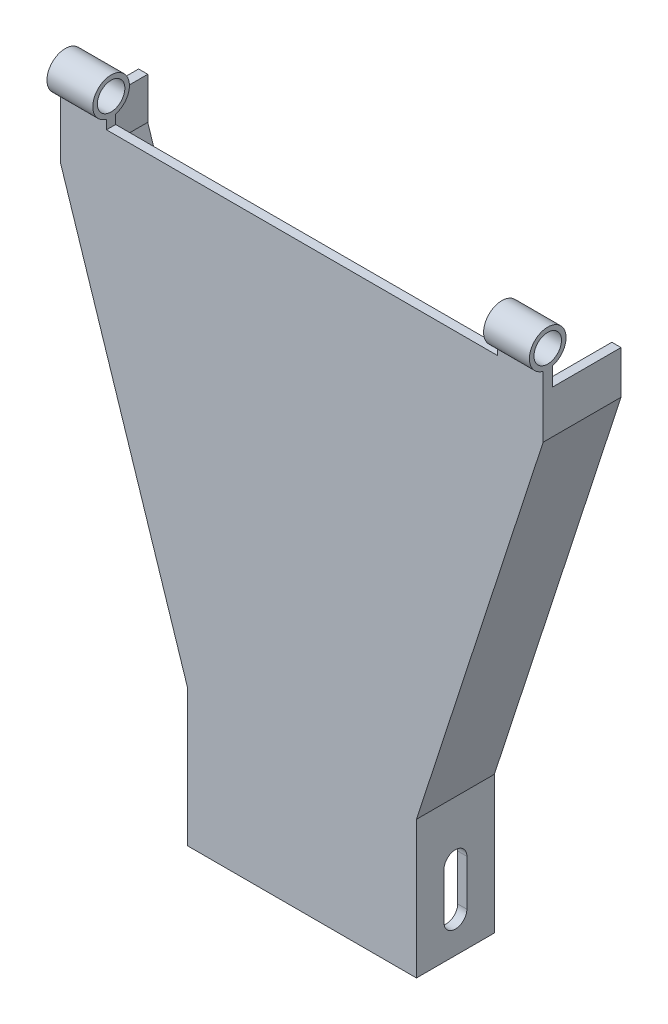
SolidWorks part; units mm, degrees
ref_plane "Front Plane" through (0, 0, 0) normal (0, 0, 1) x (1, 0, 0)
ref_plane "Top Plane" through (0, 0, 0) normal (0, 1, 0) x (1, 0, 0)
ref_plane "Right Plane" through (0, 0, 0) normal (1, 0, 0) x (0, 0, -1)
sketch "Sketch1" plane through (0, 0, 0) normal (0, 0, 1) x (1, 0, 0)
  line L1 (-52.65, -30.4) -> (-25, -115.5)
  line L2 (-25, -115.5) -> (-25, -145.5)
  line L3 (-42.65, -17) -> (-42.65, -19)
  line L4 (52.65, -30.4) -> (25, -115.5)
  line L5 (-42.65, -19) -> (42.65, -19)
  line L6 (42.65, -19) -> (42.65, -17)
  line L7 (25, -115.5) -> (25, -145.5)
  line L9 (52.65, -17) -> (52.65, -30.4)
  line L11 (25, -145.5) -> (-25, -145.5)
  line L13 (-52.65, -30.4) -> (-52.65, -17)
  line L14 (16, -30.4) -> (-16, -30.4) construction
  line L16 (42.15, -14) -> (53.15, -14) construction
  line L20 (18.1, -17) -> (42.15, -17) construction
  line L21 (-115.8448, -115.5) -> (115.8448, -115.5) construction
  line L22 (42.65, -17) -> (52.65, -17)
  line L23 (-52.65, -17) -> (-42.65, -17)
  line L24 (-42.15, -17) -> (-18.1, -17) construction
  line L25 (-42.15, -14) -> (-53.15, -14) construction
  circle A1 centre (0, 0) radius 115.5 construction
  point P16 (47.65, -14)
  point P22 (0, -115.5)
  point P26 (0, -145.5)
  point P28 (47.65, -17)
  point P31 (-47.65, -14)
  point P32 (-47.65, -17)
  dimension "pelletOutletTrackHingeWidth" = 10
  dimension "hingeClearance" = 2
  dimension "pelletOutletTrackEndingLength" = 30
  dimension "pelletOutletTrackEndingWidth" = 50
extrude "Boss-Extrude1" add sketch "Sketch1" along normal mid plane 2 from offset 4
sketch "Sketch2" plane through (52.65, 0, 0) normal (1, 0, 0) x (0, 0, -1)
  line L1 (-5, -17) -> (-3, -17) construction
  circle A0 centre (-4, -13.127) radius 3
  circle A1 centre (-4, -13.127) radius 4
  point P6 (-4, -17)
  dimension "pelletOutletTrackMountingPlateHingeDiameter" = 6
  dimension "D2" = 8
extrude "Boss-Extrude2" add sketch "Sketch2" against normal blind 10
sketch "Sketch3" plane through (0, 0, 3) normal (0, 0, -1) x (-1, 0, 0)
  line L1 (25, -145.5) -> (-25, -145.5) construction
  line L5 (-23, -145.5) -> (-25, -145.5)
  line L12 (-52.65, -30.4) -> (-52.65, -17) construction
  line L13 (-52.65, -30.4) -> (-52.65, -21)
  line L14 (-50.65, -30.0832) -> (-50.65, -21)
  line L15 (-52.65, -21) -> (-50.65, -21)
  line L19 (-42.65, -19) -> (42.65, -19) construction
  line L20 (-25, -115.5) -> (-52.65, -30.4) construction
  line L21 (-25, -115.5) -> (-52.65, -30.4)
  line L22 (-25, -145.5) -> (-25, -115.5) construction
  line L23 (-25, -145.5) -> (-25, -115.5)
  line L24 (-50.65, -30.0832) -> (-23, -115.1832)
  line L25 (-23, -115.1832) -> (-23, -145.5)
  dimension "D2" = 2
  dimension "D3" = 2
  dimension "D1" = 2
  dimension "D4" = 2
extrude "Boss-Extrude3" add sketch "Sketch3" along normal blind 15
sketch "Sketch7" plane through (25, 0, 0) normal (1, 0, 0) x (0, 0, -1)
  line L0 (3.5, -128) -> (3.5, -138) construction
  line L1 (6, -128) -> (6, -138)
  line L2 (1, -128) -> (1, -138)
  line L3 (10.0628, -140.5) -> (-3.0628, -140.5) construction
  line L4 (-5, -145.5) -> (12, -145.5) construction
  arc A0 (6, -128) -> (1, -128) centre (3.5, -128) ccw
  arc A1 (1, -138) -> (6, -138) centre (3.5, -138) ccw
  point P2 (3.5, -133)
  point P9 (3.5, -140.5)
  point P13 (3.5, -145.5)
  dimension "D1" = 5
  dimension "D2" = 10
  dimension "D3" = 5
extrude "Cut-Extrude1" cut sketch "Sketch7" against normal through all
mirror "Mirror2" about plane through (0, 0, 0) normal (1, 0, 0) of "Cut-Extrude1", "Boss-Extrude3", "Boss-Extrude2"
equation "\"pelletOutletTrackHingeWidth@Sketch1\" = \"pelletOutletTrackHingeWidth\""
equation "\"generalFittingTolerance\"= 0.1mm'The general fitting tolerance between contacting parts"
equation "\"pelletWidth\"= 13mm'The Width of the pellet to be dispensed"
equation "\"pelletLength\"= 26mm'The length of the pellet to be dispensed"
equation "\"pelletThickness\"= 13mm'The Thickness of the pellet to be dispensed"
equation "\"pelletRadius\"= 10mm'The roundness / radius of the pellet to be dispensed"
equation "\"rotatingPlateDiameter\"= 100mm'the diameter of the rotating plate"
equation "\"rotatingPlateHeight\"= (\"pelletThickness\"*0.9)'The thickness of the rotating plate"
equation "\"rotatingPlateDiameterAllowance\"= 0.5mm'Allowance around the edge of the rotating plate"
equation "\"rotatingPlatePelletSlotLength\"= \"pelletLength\"*1.3'The length of the slot where a pellet will be captured"
equation "\"rotatingPlatePelletSlotWidth\"= \"pelletWidth\"*1.3'The width of the slot where a pellet will be captured"
equation "\"rotatingPlateNumberOfPelletSlots\"= ( (2*pi*(\"rotatingPlateDiameter\"/2)) / ((\"rotatingPlatePelletSlotLength\"*1.1)*3) )'The maximum number of pellet slots allows in the rotating plate for proper spacing"
equation "\"rotatingPlateAgitatorDiameter\"= ( \"rotatingPlateDiameter\"-((\"pelletWidth\"*1.3)*2.5) )'The diameter of the \"agitator\" section of the rotating plate"
equation "\"rotatingPlateAgitatorHeight\"= 80mm'The height of the \"agitator\" section of the rotating plate"
equation "\"rotatingPlateAgitatorTopRoundingRadius\"= 6mm'The rounding radius of the top of the \"agitator\" section of the rotating plate"
equation "\"rotatingPlateAgitatorBladeThickness\"= 4mm'The thickness of the blade on the \"agitator\" section of the rotating plate"
equation "\"rotatingPlateAgitatorBladeDistance\"= ( (\"rotatingPlateAgitatorDiameter\"+ 20mm) - (\"rotatingPlateAgitatorDiameter\") )'The distance offset of the blade from the surface of the \"agitator\" section of the rotating plate"
equation "\"rotatingPlateAgitatorBladeBottomGap\"= ( \"pelletThickness\"*1.2 )'The gap between the bottom of the blade and the base of the plate on the \"agitator\" section of the rotating plate"
equation "\"rotatingPlateAgitatorBladesNumber\"= ( 3 )'The number of blades on the \"agitator\" section of the rotating plate"
equation "\"hopperBaseInnerDiameter\"= (\"rotatingPlateDiameter\") + (\"rotatingPlateDiameterAllowance\"*2)'Diameter of the Base of the hopper where it meets the motor mount + rotating plate"
equation "\"hopperBaseOuterDiameter\"= (\"hopperBaseInnerDiameter\" + (\"hopperTankWallThickness\"*2) + 60mm)'Diameter of the Base of the hopper where it meets the motor mount + rotating plate"
equation "\"hopperBaseChamferAngle\"= 60deg'Angle of the chamfer of the Hopper base Toward the plate"
equation "\"hopperBaseLipOverhang\"= 5mm'The overhang amount of the hopper base lip"
equation "\"hopperBaseLipDepth\"= 5mm'The depth of the hopper base's overhang lip"
equation "\"hopperBaseLockNotchWidth\"= 10mm'The width of the hopper base \"lock\" notch to prevent rotation"
equation "\"hopperBaseLockNotchHeight\"= 10mm'The height of the hopper base \"lock\" notch to prevent rotation"
equation "\"hopperBaseRearNotchHeight\"= 8mm'The height of the rear snap-lock notch on the hopper base"
equation "\"hopperBaseRearNotchWidth\"= 8mm'The width of the rear snap-lock notch on the hopper base"
equation "\"hopperTankWallThickness\"= 5mm'The wall thickness of the hopper tank where pellet reserve will be stored"
equation "\"hopperTankDiameter\"= ( \"rotatingPlateDiameter\"*1.8 )'**Must be greater than \"rotatingPlateDiameter\" -- The inner diameter of the hopper tank where pellet reserve will be stored"
equation "\"hopperTankHeight\"= 200mm'The height of the hopper tank where pellet reserve will be stored"
equation "\"hopperTankCoverThickness\"= 10mm'The thickness of the Hopper Tank's cover"
equation "\"hopperTankCoverHandleLength\"= 60mm'The length of the handles on the hopper tank cover"
equation "\"hopperTankCoverHandleWidth\"= 20mm'The width of the handles on the hopper tank cover, defined as the offset from the cover's main edge"
equation "\"hopperBasePelletBlockerMountingSlotWidth\"= 5mm'The width of the pellet blocker mounting slot on the hopper base"
equation "\"hopperBasePelletBlockerMountingSlotOffsetFromTopOfChamfer\"= 15mm'The distance offset of the top of the pellet blocker mounting slot from the top of the hopper base chamfer"
equation "\"hopperBasePelletBlockerMountingSlotOffsetFromBottomOfChamfer\"= 10mm'The distance offset of the bottom of the pellet blocker mounting slot from the bottom of the hopper base chamfer"
equation "\"motorMountOffset\"= 30mm'The distance offset of the motor mount part from the hopper tank's outer edge"
equation "\"motorMountHeight\"= (\"motorHeight\" + \"motorFacePlateThickness\" + 0mm)'The height / thickness of the motor mount part"
equation "\"motorMountPelletThroughHoleLength\"= 40mm'The length of the pellet throughhole that routes through the motor mount and other parts"
equation "\"motorMountPelletThroughHoleWidth\"= 20mm'The width of the pellet throughhole that routes through the motor mount and other parts"
equation "\"motorDiameter\"= 35mm'The Diameter of the main motor unit"
equation "\"motorHeight\"= 13.4mm'The height of the main motor unit"
equation "\"motorConnectorWidth\"= 10mm'The width of the motor's electrical cable connector"
equation "\"motorConnectorLength\"= 8mm'The length of the motor's electrical cable connector"
equation "\"motorConnectorHeight\"= 5mm'The height of the motor's electrical cable connector"
equation "\"motorFacePlateLength\"= 50mm'The length of the motor faceplate"
equation "\"motorFacePlateWidth\"= 10mm'The width of the motor faceplate"
equation "\"motorFacePlateThickness\"= 1mm'The thickness of the motor faceplate"
equation "\"motorFacePlateCenterRadius\"= 20mm'The rounding radius of the motor faceplate center"
equation "\"motorFacePlateEndRadius\"= 10mm'The rounding radius of the motor faceplate ends"
equation "\"motorFacePlateMountingHoleDiameter\"= 6mm'The diameter of the motor faceplate's mounting holes"
equation "\"motorFacePlateMoutingHoleDistanceBetweenHoles\"= 42mm'The distance between the center of the mounting holes"
equation "\"motorSpindleDiameter\"= 2mm'The diameter of the motor spindle"
equation "\"motorSpindleFlatFaceLength\"= 1.5mm'The length of the flat face of the motor spindle"
equation "\"motorSpindleHeight\"= 9mm'The height of the motor spindle from the face of the motor"
equation "\"motorSpindleMountDiameter\"= 12mm'The diameter of the raised mount section of the motor where the spindle is attached"
equation "\"motorSpindleMountHeight\"= 1.5mm'The height of the raised mount section of the motor where the spindle is attached"
equation "\"irBeamUnitLength\"=20mm'The legth of the IR beam unit"
equation "\"irBeamUnitWidth\"=10mm'The width of the IR beam unit"
equation "\"irBeamUnitHeight\"=8mm'The height of the IR beam unit"
equation "\"irBeamUnitSlotWidth\"=2.03mm'The width of the slots on the outside of the IR beam unit"
equation "\"irBeamUnitSlotLength\"=5.10mm'The length of the slots of the outside of the IR beam unit"
equation "\"irBeamUnitSlotDepth\"=0.76mm'The depth of the slots on the outside of the IR beam unit"
equation "\"irBeamUnitSlotChamferAngle\"=45deg'The angle of the \"end\" of the slot on the outside of the IR beam unit"
equation "\"irBeamUnitSideSlotsDistanceFromBottom\"=3.98mm'The distance of the side slots on the outside of the IR beam unit from the bottom edge of the unit"
equation "\"irBeamUnitMountHoleDistanceFromBottom\"=5mm'The distance of the center mounting throughhole of the IR beam unit from the bottom edge of the unit"
equation "\"irBeamUnitMountHoleDiameter\"=2.40mm'The diameter of the center mounting throughhole of the IR beam unit"
equation "\"irBeamUnitMountHoleChamferDiameter\"=5.30mm'The diameter of the chamfer of the center mounting throughole of the IR beam unit"
equation "\"irBeamUnitMountHoleChamferDepth\"=2.65mm'The depth of the chamfer of the center mounting throughole of the IR beam unit"
equation "\"irBeamUnitLEDDistanceFromBottom\"=15mm'The distance of the center of the LED from the bottom edge of the IR beam unit"
equation "\"irBeamUnitLEDMountDiameter\"=8mm'The diameter of the LED mounting base of the IR beam unit"
equation "\"irBeamUnitLEDMountHeight\"=1.02mm'The height of the LED mounting base of the IR beam unit"
equation "\"irBeamUnitLEDDiameter\"=3.00mm'The diameter of the LED of the IR beam unit"
equation "\"irBeamUnitLEDFlatSectionHeight\"=0.65mm'The height of the \"flat\" section of the LED of the IR beam unit"
equation "\"irBeamUnitLEDDomeSectionDiameter\"=\"irBeamUnitLEDDiameter\"'The diameter of the \"domed\" section of the LED of the IR beam unit"
equation "\"irBeamUnitMountingPlateThickness\"=2mm'The thickness of the IR beam unit mounting plate"
equation "\"irBeamUnitMountingPlateAdjustmentSlotLength\"=10mm'The length of the variable/adjustable mounting slot of the IR beam unit mounting plate"
equation "\"pelletBlockerBaseWidth\"= (\"rotatingPlatePelletSlotWidth\"+\"rotatingPlateDiameterAllowance\")*1.1'The width of the base of the pellet blocker where it meets the rotating plate & pellet slot"
equation "\"pelletBlockerBaseLength\"= \"rotatingPlatePelletSlotLength\"*1.1'The length of the base of the pellet blocker where it meets the rotating plate & pellet slot"
equation "\"pelletBlockerBaseRoundingRadius\"= \"pelletWidth\"*0.5'The rounding radius of the base of the pellet blocker where it meets the rotating plate & pellet slot"
equation "\"pelletBlockerBaseHeight\"= \"rotatingPlateAgitatorBladeBottomGap\"*0.75'The height of the base of the pellet blocker where it meets the rotating plate & pellet slot"
equation "\"pelletBlockerNeckLength\"= 50mm'The length of the neck of the pellet blocker"
equation "\"pelletBlockerNeckTopRoundingRadius\"=2mm'The rounding radius of the top of the neck of the pellet blocker"
equation "\"pelletOutletTrackMountingPlateThickness\"= 2mm'The thickness of the Pellet Outlet Track Mounting Plate"
equation "\"pelletOutletTrackMountingPlateHingeHeight\"= (\"irBeamUnitWidth\" + \"irBeamUnitMountingPlateThickness\" + 2mm )'The height of the bottom of the hinge of the Pellet Outlet Mounting Plate"
equation "\"pelletOutletTrackMountingPlateHingeDiameter\"= 6mm'The inner diameter of the hinge on the Pellet Outlet Mounting Plate"
equation "\"pelletOutletTrackMountingPlateHingeOffsetFromHoleDistance\"= (\"pelletOutletTrackMountingPlateHingeDiameter\" + \"pelletOutletTrackMountingPlateThickness\" + 4mm)'The distance offset of the hinge of the Pellet Outlet Mounting Plate from the plate's mounting hole position"
equation "\"pelletOutletTrackHingeWidth\"= 10mm'The width of the pellet outlet track's hinge which mates with the hinge on the mounting plate"
equation "\"pelletOutletTrackHingeOffsetFromIRBeamUnitEdge\"= 6mm'The distance offset of the pelletOutletTrack's mating hinge from the edge of the IR Beam Unit"
equation "\"pelletOutletTrackEndingWidth\"= 50mm'The width of the pellet outlet Track at the end of the Track"
equation "\"pelletOutletTrackThickness\"= 2mm'The thickness of the pellet outlet Track"
equation "\"D19@Boss-Extrude1\"=(\"pelletOutletTrackMountingPlateHingeDiameter\"+\"pelletOutletTrackMountingPlateThickness\")/2"
equation "\"D1@Boss-Extrude2\"=\"pelletOutletTrackHingeWidth\""
equation "\"pelletOutletTrackEndingLength\"= 30mm'The length of pellet outlet Track at the end of the Track"
equation "\"pelletOutletTrackEndingWidth@Sketch1\" = \"pelletOutletTrackEndingWidth\""
equation "\"pelletOutletTrackEndingLength@Sketch1\" = \"pelletOutletTrackEndingLength\""
equation "\"pelletOutletTrackMountingPlateHingeDiameter@Sketch2\" = \"pelletOutletTrackMountingPlateHingeDiameter\""
equation "\"D2@Sketch2\"=\"pelletOutletTrackThickness\"+\"pelletOutletTrackMountingPlateHingeDiameter\""
equation "\"D3@Sketch3\"=\"pelletOutletTrackThickness\""
equation "\"D2@Sketch3\"=\"pelletOutletTrackThickness\""
equation "\"D1@Sketch3\"=\"pelletOutletTrackThickness\""
equation "\"D4@Sketch3\"=\"pelletOutletTrackThickness\""
equation "\"D1@Boss-Extrude3\"= \"pelletOutletTrackWallHeight\""
equation "\"pelletOutletTrackWallHeight\"= 15mm'The height of the side walls of the pellet outlet Track"
equation "\"baseStandMountingFaceHeight\"= 10mm'The height / thickness of the mounting face between the Base Stand and the Motor Mount parts"
equation "\"baseStandOpeningAngle\"= 55deg'The angle of the opening in the front of the Base Stand to allow for unobstructed pellet outlet"
equation "\"baseStandWallThickness\"= 10mm'The wall thickness of the Base Stand"
equation "\"baseStandHeight\"= 100mm'The overall height of the Base Stand part"
equation "\"baseStandFootDiameterOffset\"= 40mm'The distance offset of the Base Stand's foot ring"
equation "\"baseStandFootHeight\"= 20mm'The height / thickness of the Base Stand's foot ring"
equation "\"hingeClearance@Sketch1\" = \"pelletOutletTrackThickness\""
